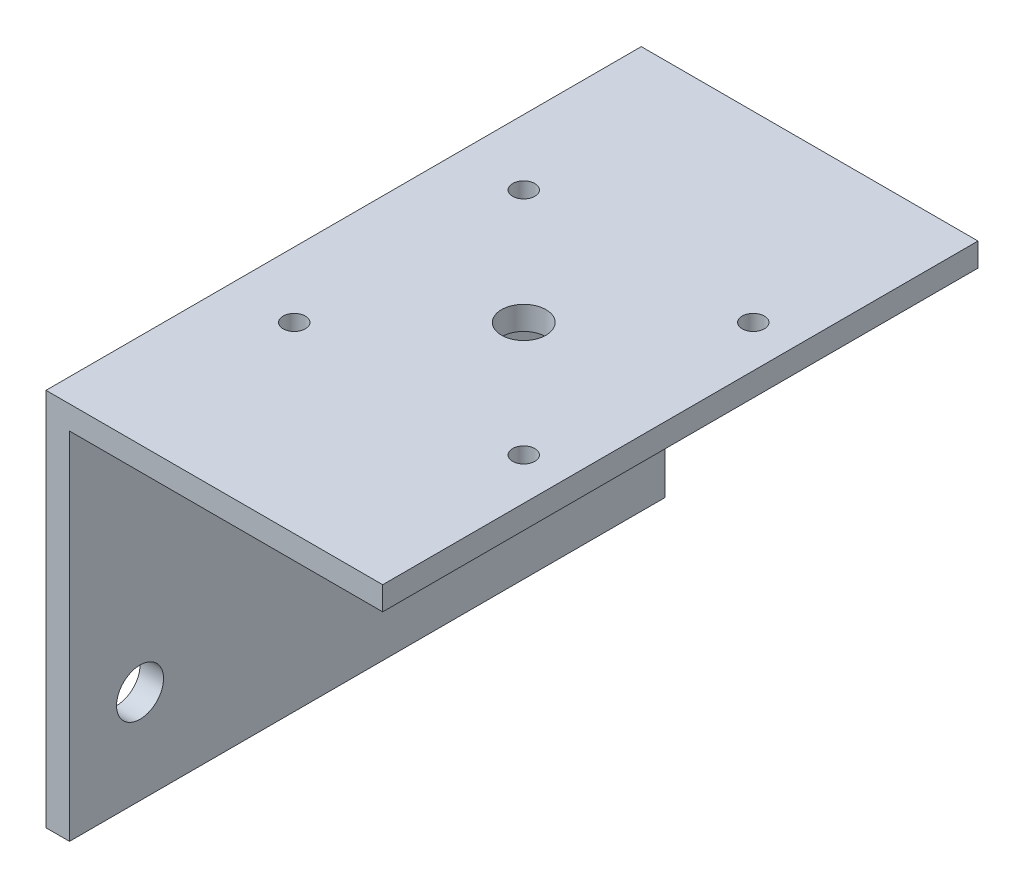
SolidWorks part; units mm, degrees
ref_plane "Front Plane" through (0, 0, 0) normal (0, 0, 1) x (1, 0, 0)
ref_plane "Top Plane" through (0, 0, 0) normal (0, 1, 0) x (1, 0, 0)
ref_plane "Right Plane" through (0, 0, 0) normal (1, 0, 0) x (0, 0, -1)
sketch "Sketch1" plane through (0, 0, 0) normal (0, 0, 1) x (1, 0, 0)
  line L1 (0, 0) -> (3.175, 0)
  line L2 (0, 0) -> (0, 51.175)
  line L3 (0, 51.175) -> (45.475, 51.175)
  line L4 (45.475, 48) -> (45.475, 51.175)
  line L7 (45.475, 48) -> (3.175, 48)
  line L8 (3.175, 0) -> (3.175, 48)
  dimension "D1" = 51.175
  dimension "D2" = 45.475
  dimension "D3" = 3.175
  dimension "D4" = 3.175
extrude "Boss-Extrude1" add sketch "Sketch1" along normal blind 80.4
sketch "Sketch2" plane through (3.175, 0, 0) normal (1, 0, 0) x (0, 0, -1)
  line L0 (-80.4, 0) -> (0, 0) construction
  line L1 (0, 0) -> (0, 48) construction
  line L2 (-80.4, 0) -> (-80.4, 48) construction
  circle A0 centre (-70.875, 12.7) radius 3.175
  circle A1 centre (-9.525, 12.7) radius 3.175
  dimension "D1" = 6.35
  dimension "D2" = 12.7
  dimension "D3" = 12.7
  dimension "D4" = 9.525
  dimension "D5" = 9.525
extrude "Cut-Extrude1" cut sketch "Sketch2" against normal through all
sketch "Sketch3" plane through (0, 51.175, 0) normal (0, 1, 0) x (1, 0, 0)
  line L0 (0, -40.2) -> (45.475, -40.2) construction
  line L1 (0, -80.4) -> (0, 0) construction
  line L2 (45.475, -80.4) -> (45.475, 0) construction
  line L3 (24.325, -80.4) -> (24.325, 0) construction
  line L4 (45.475, -80.4) -> (0, -80.4) construction
  line L5 (45.475, 0) -> (0, 0) construction
  circle A0 centre (39.825, -55.7) radius 1.5
  circle A1 centre (8.825, -55.7) radius 1.5
  circle A2 centre (8.825, -24.7) radius 1.5
  circle A3 centre (39.825, -24.7) radius 1.5
  circle A4 centre (24.325, -40.2) radius 3
  dimension "D1" = 3
  dimension "D7" = 6
  dimension "D2" = 31
  dimension "D3" = 31
  dimension "D4" = 15.5
  dimension "D5" = 21.15
  dimension "D6" = 15.5
extrude "Cut-Extrude2" cut sketch "Sketch3" against normal through all
